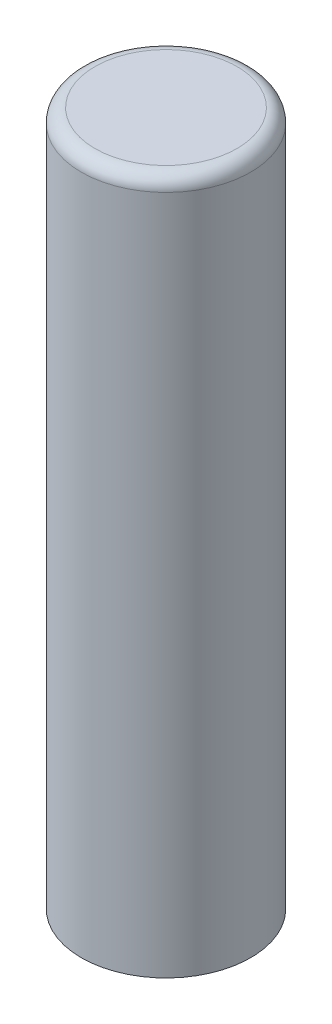
SolidWorks part; units mm, degrees
ref_plane "Front Plane" through (0, 0, 0) normal (0, 0, 1) x (1, 0, 0)
ref_plane "Top Plane" through (0, 0, 0) normal (0, 1, 0) x (1, 0, 0)
ref_plane "Right Plane" through (0, 0, 0) normal (1, 0, 0) x (0, 0, -1)
sketch "Sketch1" plane through (0, 0, 0) normal (0, 1, 0) x (1, 0, 0)
  circle A0 centre (0, 0) radius 1.55
  dimension "D1" = 3.1
extrude "Boss-Extrude1" add sketch "Sketch1" along normal blind 12.7
fillet "Fillet1" radius 0.25 1 edges at (0, 12.7, 1.55)
